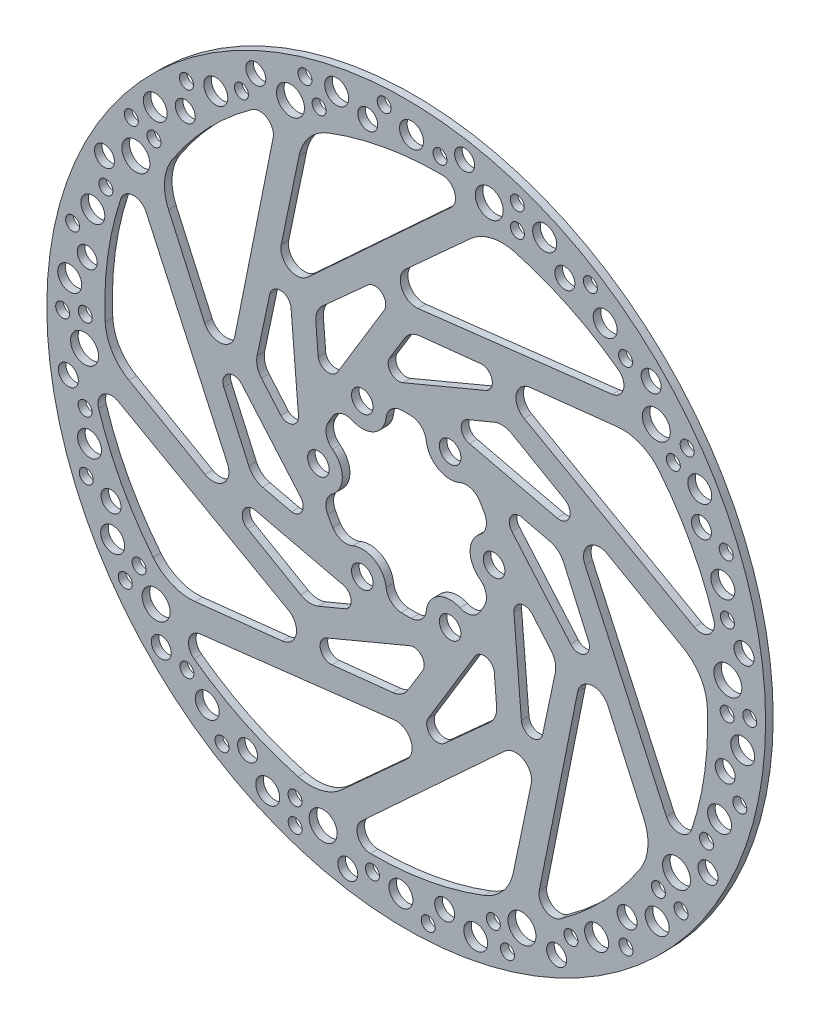
SolidWorks part; units mm, degrees
material "AISI Тип 316L нержавеющая сталь"
ref_plane "Front" through (0, 0, 0) normal (0, 0, 1) x (1, 0, 0)
ref_plane "Top" through (0, 0, 0) normal (0, 1, 0) x (1, 0, 0)
ref_plane "Right" through (0, 0, 0) normal (1, 0, 0) x (0, 0, -1)
sketch "Sketch1" plane through (0, 0, 0) normal (0, 0, 1) x (1, 0, 0)
  circle A0 centre (0, 0) radius 90
  dimension "D1" = 180
sketch "Sketch5" plane through (0, 0, 0) normal (0, 0, 1) x (1, 0, 0)
  circle A0 centre (0, 0) radius 90
  circle A1 centre (0, 0) radius 90 construction
extrude "Extrude2" add sketch "Sketch5" along normal blind 1.9
sketch "Sketch2" plane through (0, 0, 0) normal (0, 0, 1) x (1, 0, 0)
  line L0 (0, 0) -> (-11, 19.0526) construction
  line L1 (0, 0) -> (0, 22) construction
  line L2 (-21.0022, 34.6179) -> (-9.6329, 44.8759)
  line L3 (-5.5159, 41.4698) -> (-17.211, 22.2071)
  line L4 (-22.0393, 23.0436) -> (-22.6382, 30.5016)
  line L5 (11.2432, 72.1578) -> (-24.6773, 39.0489)
  line L6 (-31.3044, 42.8051) -> (-26.833, 64.2901)
  circle A2 centre (-11, 19.0526) radius 2.5 construction
  circle A3 centre (0, 0) radius 22 construction
  arc A4 (-9.6329, 44.8759) -> (-5.5159, 41.4698) centre (-7.824, 42.8711) cw
  arc A5 (-17.211, 22.2071) -> (-22.0393, 23.0436) centre (-19.4609, 23.5732) cw
  arc A6 (-22.6382, 30.5016) -> (-21.0022, 34.6179) centre (-17.6497, 30.9022) cw
  arc A7 (-24.6773, 39.0489) -> (-31.3044, 42.8051) centre (-27.3883, 41.9901) cw
  arc A8 (-26.833, 64.2901) -> (-19.4609, 72.9352) centre (-15.2513, 61.8797) cw
  arc A9 (11.2432, 72.1578) -> (8.9568, 78.068) centre (8.9349, 74.6622) ccw
  arc A10 (-19.4609, 72.9352) -> (8.9568, 78.068) centre (8.452, -0.3712) cw
  circle A11 centre (-28.9827, 75.2697) radius 3.5
  circle A12 centre (-17.4064, 82.9421) radius 3
  circle A13 centre (-25.3552, 82.2101) radius 1.75
  circle A14 centre (-21.8142, 77.4148) radius 1.75
  circle A15 centre (-9.6329, 80.8545) radius 2.5
  circle A16 centre (-5.5159, 86.0377) radius 1.75
  circle A17 centre (1.3302, 82.9421) radius 3
  circle A18 centre (8.452, 81.8174) radius 1.75
  circle A19 centre (14.6261, 84.2031) radius 2.5
  dimension "D1" = 44
  dimension "D2" = 5
  dimension "D4" = 7
  dimension "D5" = 3.5
  dimension "D6" = 6
  dimension "D7" = 5
  dimension "D3" = 30
extrude "Cut-Extrude5" cut sketch "Sketch2" along normal up to surface (1.9 mm away) up to face at (90, 0, 1.9)
pattern_circular "CirPattern3" count 10 over 360 about axis through (0, 0, 0) along (0, 0, 1) of "Cut-Extrude5"
sketch "Sketch4" plane through (0, 0, 0) normal (0, 0, 1) x (1, 0, 0)
  line L0 (-11, 19.0526) -> (0, 0) construction
  line L1 (0, 22) -> (0, 0) construction
  line L2 (0, 0) -> (-19.0526, 11) construction
  line L3 (-9.5263, 5.5) -> (0, 11) construction
  arc A0 (-13.4192, 13.5619) -> (-5.0353, 18.4023) centre (-11, 19.0526) ccw
  arc A1 (-18.3725, 12.1018) -> (-19.0526, 11) centre (0, 0) ccw
  circle A2 centre (0, 0) radius 22 construction
  arc A3 (-13.4192, 13.5619) -> (-18.3725, 12.1018) centre (-15.032, 9.9014) ccw
  arc A4 (-5.0353, 18.4023) -> (-1.2942, 21.9619) centre (-1.0589, 17.9688) cw
  arc A5 (0, 22) -> (-1.2942, 21.9619) centre (0, 0) ccw
  arc A6 (5.0353, 18.4023) -> (13.4192, 13.5619) centre (11, 19.0526) ccw
  arc A7 (13.4192, 13.5619) -> (18.3725, 12.1018) centre (15.032, 9.9014) cw
  arc A8 (19.0526, 11) -> (18.3725, 12.1018) centre (0, 0) ccw
  arc A9 (5.0353, 18.4023) -> (1.2942, 21.9619) centre (1.0589, 17.9688) ccw
  arc A10 (1.2942, 21.9619) -> (0, 22) centre (0, 0) ccw
  arc A11 (18.4545, 4.8404) -> (18.4545, -4.8404) centre (22, 0) ccw
  arc A12 (18.4545, -4.8404) -> (19.6667, -9.8601) centre (16.0909, -8.0674) cw
  arc A13 (19.0526, -11) -> (19.6667, -9.8601) centre (0, 0) ccw
  arc A14 (18.4545, 4.8404) -> (19.6667, 9.8601) centre (16.0909, 8.0674) ccw
  arc A15 (19.6667, 9.8601) -> (19.0526, 11) centre (0, 0) ccw
  arc A16 (13.4192, -13.5619) -> (5.0353, -18.4023) centre (11, -19.0526) ccw
  arc A17 (5.0353, -18.4023) -> (1.2942, -21.9619) centre (1.0589, -17.9688) cw
  arc A18 (0, -22) -> (1.2942, -21.9619) centre (0, 0) ccw
  arc A19 (13.4192, -13.5619) -> (18.3725, -12.1018) centre (15.032, -9.9014) ccw
  arc A20 (18.3725, -12.1018) -> (19.0526, -11) centre (0, 0) ccw
  arc A21 (-5.0353, -18.4023) -> (-13.4192, -13.5619) centre (-11, -19.0526) ccw
  arc A22 (-13.4192, -13.5619) -> (-18.3725, -12.1018) centre (-15.032, -9.9014) cw
  arc A23 (-19.0526, -11) -> (-18.3725, -12.1018) centre (0, 0) ccw
  arc A24 (-5.0353, -18.4023) -> (-1.2942, -21.9619) centre (-1.0589, -17.9688) ccw
  arc A25 (-1.2942, -21.9619) -> (0, -22) centre (0, 0) ccw
  arc A26 (-18.4545, -4.8404) -> (-18.4545, 4.8404) centre (-22, 0) ccw
  arc A27 (-18.4545, 4.8404) -> (-19.6667, 9.8601) centre (-16.0909, 8.0674) cw
  arc A28 (-19.0526, 11) -> (-19.6667, 9.8601) centre (0, 0) ccw
  arc A29 (-18.4545, -4.8404) -> (-19.6667, -9.8601) centre (-16.0909, -8.0674) ccw
  arc A30 (-19.6667, -9.8601) -> (-19.0526, -11) centre (0, 0) ccw
  point P17 (-4.7631, 8.25)
  dimension "D1" = 12
  dimension "D2" = 4
extrude "Cut-Extrude6" cut sketch "Sketch4" along normal up to surface (1.9 mm away) up to face at (-39.5032, 71.1596, 1.9)
hole_wizard "Ø5.4 (5.4) Diameter Hole1" positions "Sketch7" profile "Sketch6" hole size "Ø5.4" standard "BSI"
sketch "Sketch7" plane through (0, 0, 0) normal (0, 0, -1) x (-1, 0, 0)
  point P0 (11, 19.0526)
sketch "Sketch6" plane through (-11, 19.0526, 0) normal (1, 0, 0) x (0, 1, 0)
  line L0 (0, 0) -> (0, 6.6223)
  line L1 (0, 6.6223) -> (2.7, 5)
  line L2 (2.7, 5) -> (2.7, 0)
  line L5 (2.7, 0) -> (0, 0)
  line L10 (0, 6.6223) -> (-2.7, 5) construction
  line L11 (0, -6.35) -> (0, 107.95) construction
  dimension "Hole Dia." = 5.4
  dimension "Hole Depth" = 5
  dimension "Drill Angle" = 118
pattern_circular "CirPattern4" count 6 over 360 about axis through (0, 0, 0) along (0, 0, 1) of "Ø5.4 (5.4) Diameter Hole1"
